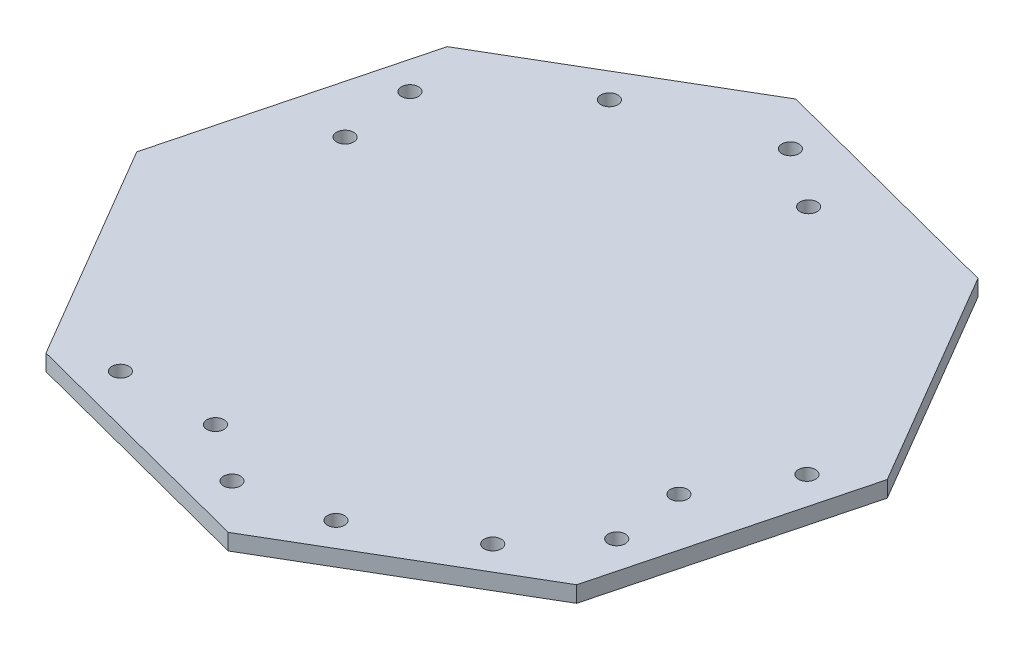
SolidWorks part; units mm, degrees
ref_plane "Front Plane" through (0, 0, 0) normal (0, 0, 1) x (1, 0, 0)
ref_plane "Top Plane" through (0, 0, 0) normal (0, 1, 0) x (1, 0, 0)
ref_plane "Right Plane" through (0, 0, 0) normal (1, 0, 0) x (0, 0, -1)
sketch "Sketch1" plane through (-113.2265, -170.1097, -309.4398) normal (0, -1, 0) x (0.8908, 0, -0.4544)
  line L0 (-0.6955, 50.8477) -> (-7.4311, -63.2537) construction
  line L1 (16.2001, -64.6487) -> (51.5924, -33.202)
  line L2 (51.5924, -33.202) -> (54.3824, 14.0603)
  line L3 (54.3824, 14.0603) -> (22.9357, 49.4527)
  line L4 (22.9357, 49.4527) -> (-24.3266, 52.2427)
  line L5 (-24.3266, 52.2427) -> (-59.719, 20.796)
  line L6 (-59.719, 20.796) -> (-62.509, -26.4664)
  line L7 (-62.509, -26.4664) -> (-31.0623, -61.8587)
  line L8 (-31.0623, -61.8587) -> (16.2001, -64.6487)
  circle A0 centre (-4.0633, -6.203) radius 57.15 construction
  dimension "D1" = 114.3
extrude "Boss-Extrude1" add sketch "Sketch1" along normal blind 3
sketch "Sketch2" plane through (0, -173.1097, 0) normal (0, -1, 0) x (1, 0, 0)
  line L0 (-142.0892, -358.8606) -> (-148.6612, -355.004) construction
  line L1 (-124.3433, -366.831) -> (-116.9692, -364.911) construction
  line L2 (-161.5472, -338.7517) -> (-168.9213, -340.6718) construction
  line L3 (-150.8161, -268.7364) -> (-143.442, -266.8163) construction
  line L4 (-122.7553, -261.4298) -> (-115.3812, -259.5098) construction
  line L5 (-104.9924, -267.0732) -> (-101.1358, -260.5012) construction
  line L6 (-87.9796, -272.6391) -> (-81.4076, -276.4957) construction
  line L7 (-73.0322, -290.6083) -> (-74.9523, -283.2342) construction
  line L8 (-65.7257, -318.6692) -> (-67.6458, -311.295) construction
  circle A0 centre (-145.3752, -356.9323) radius 1.5875
  circle A1 centre (-120.6562, -365.871) radius 1.5875
  circle A2 centre (-165.2343, -339.7117) radius 1.5875
  circle A3 centre (-147.1291, -267.7764) radius 1.5875
  circle A4 centre (-119.0682, -260.4698) radius 1.5875
  circle A5 centre (-103.0641, -263.7872) radius 1.5875
  circle A6 centre (-84.6936, -274.5674) radius 1.5875
  circle A7 centre (-73.9923, -286.9213) radius 1.5875
  circle A8 centre (-66.6857, -314.9821) radius 1.5875
extrude "Cut-Extrude1" cut sketch "Sketch2" against normal up to surface (3 mm away) up to face at (-119.6647, -170.1097, -313.119)
sketch "Sketch3" plane through (0, -170.1097, 0) normal (0, 1, 0) x (1, 0, 0)
  circle A0 centre (-163.9391, 326.3546) radius 1.5875
  circle A1 centre (-109.627, 358.226) radius 1.5875
  circle A2 centre (-75.3903, 299.8833) radius 1.5875
  circle A3 centre (-129.7024, 268.0119) radius 1.5875
extrude "Cut-Extrude2" cut sketch "Sketch3" against normal up to surface (3 mm away) up to face at (-66.6857, -173.1097, -316.5696)
